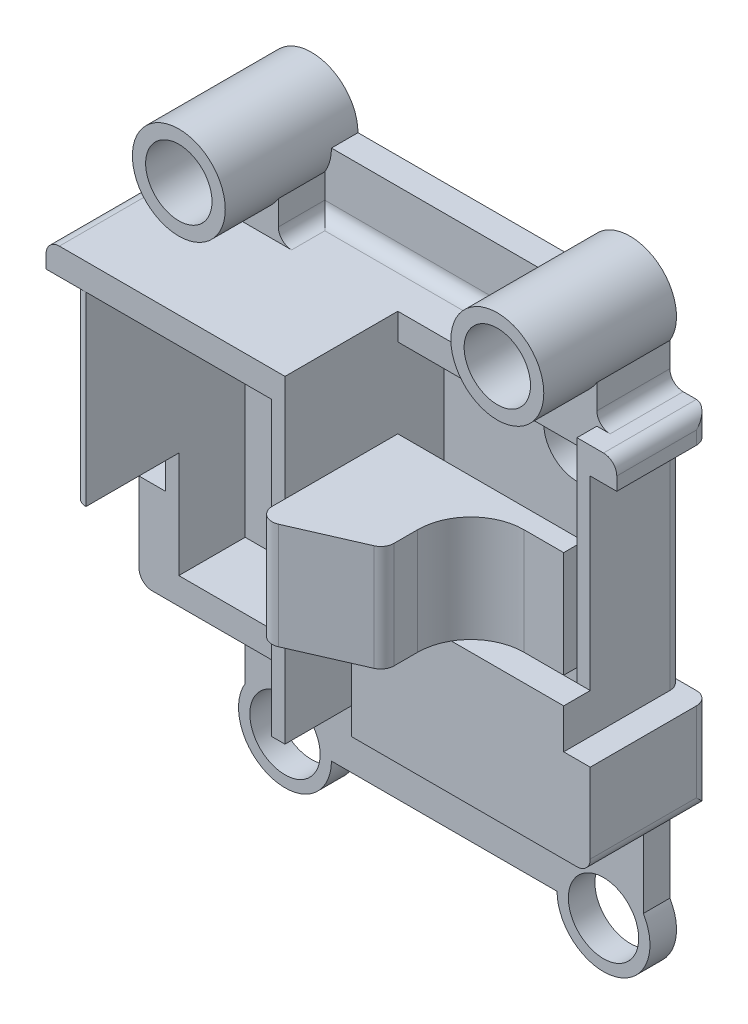
SolidWorks part; units mm, degrees
ref_plane "Front Plane" through (0, 0, 0) normal (0, 0, 1) x (1, 0, 0)
ref_plane "Top Plane" through (0, 0, 0) normal (0, 1, 0) x (1, 0, 0)
ref_plane "Right Plane" through (0, 0, 0) normal (1, 0, 0) x (0, 0, -1)
sketch "Sketch1" plane through (0, 0, 0) normal (0, 0, 1) x (1, 0, 0)
  line L0 (-15, 18.1972) -> (-15, 15.35)
  line L5 (-15, 20) -> (15, -20) construction
  line L6 (-15, -20) -> (15, 20) construction
  line L7 (-8.5, -20) -> (8.5, -20)
  line L8 (15, -18.1972) -> (15, -10.65)
  line L9 (8.5, 20) -> (-8.5, 20)
  line L10 (-15, 15.35) -> (-18, 15.35)
  line L11 (-18, 15.35) -> (-18, -10.65)
  line L12 (-18, -10.65) -> (-15, -10.65)
  line L13 (15, -10.65) -> (18, -10.65)
  line L14 (18, -10.65) -> (18, 15.35)
  line L15 (18, 15.35) -> (15, 15.35)
  line L16 (-15, -10.65) -> (-15, -18.1972)
  line L17 (15, 15.35) -> (15, 18.1972)
  circle A0 centre (12, 20) radius 2.65
  circle A1 centre (12, -20) radius 2.65
  circle A2 centre (-12, 20) radius 2.65
  circle A3 centre (-12, -20) radius 2.65
  arc A4 (-15, -18.1972) -> (-8.5, -20) centre (-12, -20) ccw
  arc A5 (-8.5, 20) -> (-15, 18.1972) centre (-12, 20) ccw
  arc A6 (15, 18.1972) -> (8.5, 20) centre (12, 20) ccw
  arc A7 (8.5, -20) -> (15, -18.1972) centre (12, -20) ccw
  point P12 (0, 0)
  point P28 (-12, 17.35)
  dimension "D1" = 5.3
  dimension "D2" = 5.3
  dimension "D4" = 5.3
  dimension "D5" = 5.3
  dimension "D9" = 7
  dimension "D10" = 7
  dimension "D11" = 7
  dimension "D12" = 7
  dimension "D3" = 40
  dimension "D6" = 40
  dimension "D7" = 15
  dimension "D8" = 24
  dimension "D13" = 12
  dimension "D14" = 20
  dimension "D15" = 30
  dimension "D16" = 20
  dimension "D17" = 3
  dimension "D18" = 3
  dimension "D19" = 2
  dimension "D20" = 26
  dimension "D21" = 26
  dimension "D22" = 2
extrude "Boss-Extrude1" add sketch "Sketch1" along normal blind 2
sketch "Sketch2" plane through (0, 0, 2) normal (0, 0, 1) x (1, 0, 0)
  line L0 (-18, 15.35) -> (0, 15.35)
  line L1 (0, 15.35) -> (0, 13.5)
  line L2 (-1, 13.35) -> (-15, 13.35)
  line L3 (-15, 13.35) -> (-15, -8.65)
  line L7 (-18, -10.65) -> (-18, 15.35)
  line L8 (-15, -8.65) -> (-1, -8.65)
  line L10 (0, -10.65) -> (-18, -10.65)
  line L15 (0, 13.5) -> (0, -7.5)
  line L16 (-1, -8.65) -> (-1, 13.35)
  line L21 (0, -10.65) -> (0, -7.5)
  dimension "D1" = 2
  dimension "D2" = 3
  dimension "D3" = 2
  dimension "D4" = 1
  dimension "D5" = 14
extrude "Boss-Extrude2" add sketch "Sketch2" along normal blind 12
sketch "Sketch3" plane through (0, 0, 14) normal (0, 0, 1) x (1, 0, 0)
  line L0 (-18, -0.65) -> (-15, -0.65)
  line L1 (-18, 15.35) -> (-18, -10.65) construction
  line L2 (-15, 13.35) -> (-15, -8.65) construction
  line L5 (-18, -10.65) -> (-18, -0.65)
  line L6 (-15, -8.65) -> (0, -8.65)
  line L8 (0, -8.65) -> (0, -10.65)
  line L10 (-18, -10.65) -> (0, -10.65)
  line L12 (-15, -8.65) -> (-15, -0.65)
  dimension "D1" = 10
extrude "Cut-Extrude1" cut sketch "Sketch3" against normal blind 7
sketch "Sketch4" plane through (0, 0, 2) normal (0, 0, 1) x (1, 0, 0)
  line L0 (18, -10.65) -> (18, 15.35)
  line L1 (18, 15.35) -> (15, 15.35)
  line L2 (15, 13.35) -> (15, -7.65)
  line L3 (15, -7.65) -> (12, -10.65)
  line L4 (12, -10.65) -> (18, -10.65)
  line L5 (0, -10.65) -> (3, -10.65)
  line L6 (3, -10.65) -> (0, -7.65)
  line L7 (0, -8.65) -> (0, 15.35) construction
  line L8 (0, -7.65) -> (0, -10.65)
  line L9 (15, 15.35) -> (0, 15.35)
  line L10 (0, 15.35) -> (0, 13.35)
  line L11 (0, 13.35) -> (15, 13.35)
  dimension "D1" = 3
  dimension "D2" = 3
  dimension "D3" = 3
  dimension "D4" = 2
extrude "Boss-Extrude3" add sketch "Sketch4" along normal blind 5
sketch "Sketch6" plane through (0, 0, 2) normal (0, 0, 1) x (1, 0, 0)
  circle A4 centre (12, 20) radius 2.5
  circle A5 centre (12, 20) radius 3.5
  circle A6 centre (-12, 20) radius 2.5
  circle A7 centre (-12, 20) radius 3.5
extrude "Boss-Extrude4" add sketch "Sketch6" along normal blind 8
sketch "Sketch7" plane through (18, 0, 0) normal (1, 0, 0) x (0, 0, -1)
  line L0 (-7, -10.65) -> (-9, -10.65)
  line L1 (-9, -10.65) -> (-9, -0.65)
  line L2 (-9, -0.65) -> (-7, -0.65)
  line L3 (-7, -10.65) -> (-7, 15.35) construction
  line L4 (-7, -0.65) -> (-7, -10.65)
  dimension "D1" = 10
  dimension "D2" = 2
extrude "Boss-Extrude5" add sketch "Sketch7" against normal blind 18
sketch "Sketch8" plane through (0, 0, 2) normal (0, 0, 1) x (1, 0, 0)
  line L0 (-15, 18.1972) -> (-15, 15.35)
  line L1 (-15, 15.35) -> (-9, 15.35)
  line L2 (15, 15.35) -> (-15, 15.35) construction
  line L3 (-9, 15.35) -> (-9, 18.1972)
  line L4 (15, 18.1972) -> (15, 15.35)
  line L6 (9.1074, 15.35) -> (9.1074, 18.0295)
  line L7 (15, 15.35) -> (9.1074, 15.35)
  arc A0 (-15, 18.1972) -> (-8.5, 20) centre (-12, 20) ccw construction
  arc A1 (-15, 18.1972) -> (-9, 18.1972) centre (-12, 20) ccw
  circle A2 centre (12, 20) radius 3.5 construction
  arc A3 (9.1074, 18.0295) -> (15, 18.1972) centre (12, 20) ccw
  arc A4 (8.5, 20) -> (15, 18.1972) centre (12, 20) ccw construction
  point P4 (-12, 20)
  point P16 (12, 20)
  dimension "D1" = 3
  dimension "D2" = 3
extrude "Boss-Extrude6" add sketch "Sketch8" along normal blind 3.5
sketch "Sketch9" plane through (0, 0, 7) normal (0, 0, 1) x (1, 0, 0)
  line L1 (0, 15.35) -> (15, 15.35)
  line L2 (0, 15.35) -> (0, 13.35)
  line L3 (0, 13.35) -> (15, 13.35)
  line L4 (15, 15.35) -> (15, 13.35)
extrude "Cut-Extrude2" cut sketch "Sketch9" against normal blind 1.5
sketch "Sketch10" plane through (0, 0, 2) normal (0, 0, 1) x (1, 0, 0)
  circle A0 centre (10, 10) radius 2.5
  point P2 (12, 20)
  dimension "D3" = 5
  dimension "D1" = 10
  dimension "D2" = 2
extrude "Cut-Extrude3" cut sketch "Sketch10" against normal through all
sketch "Sketch11" plane through (0, 0, 14) normal (0, 0, 1) x (1, 0, 0)
  line L0 (-18, 15.35) -> (-18, -0.65) construction
  line L1 (-18, 13.35) -> (-16, 13.35)
  line L2 (-18, 13.35) -> (-18, -3.65)
  line L3 (-18, -3.65) -> (-16, -3.65)
  line L4 (-16, 13.35) -> (-16, -3.65)
  line L5 (0, 15.35) -> (-18, 15.35) construction
  line L7 (18, -0.65) -> (18, 15.35) construction
  line L12 (18, 13.35) -> (16, 13.35)
  line L13 (18, 13.35) -> (18, -3.65)
  line L14 (18, -3.65) -> (16, -3.65)
  line L15 (16, 13.35) -> (16, -3.65)
  line L16 (18, 15.35) -> (15, 15.35) construction
  dimension "D1" = 2
  dimension "D2" = 17
  dimension "D3" = 2
  dimension "D4" = 2
  dimension "D5" = 2
  dimension "D6" = 17
extrude "Cut-Extrude4" cut sketch "Sketch11" against normal through all
fillet "Fillet1" radius 1 21 edges at (-15.5, -0.65, 14) (13.5, -10.65, 2) (18, -7.15, 0) (-9, 15.35, 3.75) (0.0537, 15.35, 2) (9.1074, 15.35, 3.75) (-18, 14.35, 0) (18, 14.35, 0) (-18, -7.15, 0) (-16, 6.35, 14) (-16, 4.85, 0) (16, 4.85, 0) (-15, 15.35, 2.75) (15, 15.35, 2.75) (18, 15.35, 3.5) (18, -10.65, 4.5) (15, -10.65, 1) (-15, -10.65, 1) (-18, 15.35, 7) (-6, -10.65, 2) (-18, -10.65, 3.5)
sketch "Sketch12" plane through (0, 0, 5.5) normal (0, 0, 1) x (1, 0, 0)
  line L0 (0, -0.65) -> (16, -0.65) construction
  line L1 (0, 7.35) -> (7, 7.35)
  line L2 (0, 7.35) -> (0, -0.65)
  line L3 (0, -0.65) -> (7, -0.65)
  line L4 (7, 7.35) -> (7, -0.65)
  line L5 (0, -7.65) -> (0, 13.35) construction
  point P7 (0, 7.6401)
  point P10 (0, 0)
  dimension "D1" = 8
  dimension "D2" = 7
extrude "Boss-Extrude7" add sketch "Sketch12" along normal blind 11 separate body
sketch "Sketch16" plane through (0, 7.35, 0) normal (0, 1, 0) x (1, 0, 0)
  line L0 (16, -9.5) -> (0, -16.5)
  line L2 (0, -16.5) -> (16, -16.5)
  line L3 (16, -16.5) -> (16, -9.5)
  point P2 (16, -9.5408)
  dimension "D1" = 2.5
  dimension "D2" = 2.5
extrude "Cut-Extrude5" cut sketch "Sketch16" against normal up to next (8 mm away)
sketch "Sketch19" plane through (7, 0, 0) normal (1, 0, 0) x (0, 0, -1)
  line L0 (-13.4375, 7.35) -> (-5.5, 7.35) construction
  line L1 (-5.5, 7.35) -> (-7, 7.35)
  line L2 (-5.5, 7.35) -> (-5.5, -0.65)
  line L3 (-5.5, -0.65) -> (-7, -0.65)
  line L4 (-7, 7.35) -> (-7, -0.65)
  line L5 (-13.4375, -0.65) -> (-5.5, -0.65) construction
  line L6 (-5.5, -0.65) -> (-5.5, 7.35) construction
  dimension "D1" = 1.5
fillet "Fillet2" radius 1 2 edges at (0, 3.35, 16.5) (7, 3.35, 13.4375)
extrude "Boss-Extrude18" add sketch "Sketch19" along normal blind 7
fillet "Fillet3" radius 4 1 edges at (7, 3.35, 7)
other "Save Bodies1"
